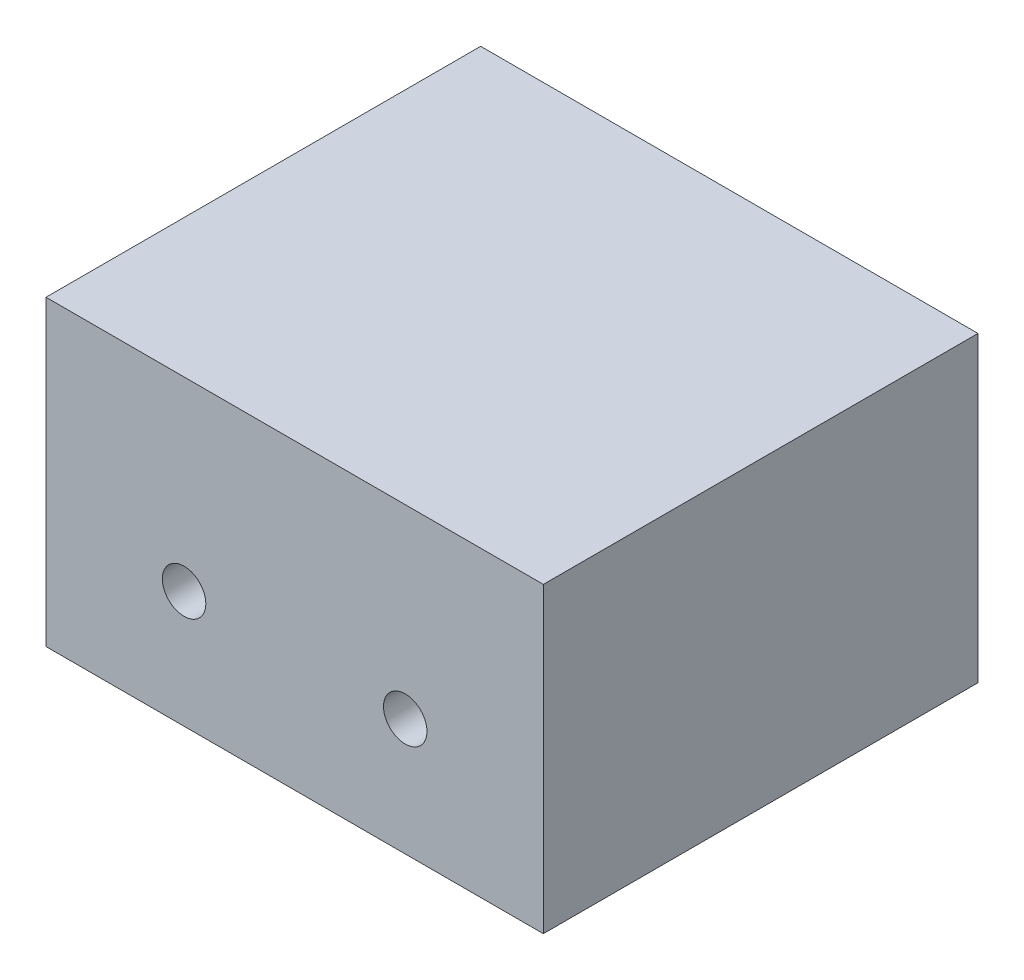
SolidWorks part; units mm, degrees
material "6061 Alloy"
ref_plane "Front Plane" through (0, 0, 0) normal (0, 0, 1) x (1, 0, 0)
ref_plane "Top Plane" through (0, 0, 0) normal (0, 1, 0) x (1, 0, 0)
ref_plane "Right Plane" through (0, 0, 0) normal (1, 0, 0) x (0, 0, -1)
sketch "Sketch1" plane through (0, 0, 0) normal (0, 1, 0) x (1, 0, 0)
  line L1 (-28.605, -25) -> (28.605, -25)
  line L2 (-28.605, -25) -> (-28.605, 25)
  line L3 (-28.605, 25) -> (28.605, 25)
  line L4 (28.605, -25) -> (28.605, 25)
  line L5 (-28.605, -25) -> (28.605, 25) construction
  line L6 (-28.605, 25) -> (28.605, -25) construction
  point P0 (0, 0)
  dimension "D1" = 57.21
  dimension "D2" = 50
extrude "Boss-Extrude1" add sketch "Sketch1" along normal blind 34.8
sketch "Sketch2" plane through (0, 0, 25) normal (0, 0, 1) x (1, 0, 0)
  line L0 (0, 34.8) -> (0, 0) construction
  line L1 (-28.605, 34.8) -> (28.605, 34.8) construction
  line L2 (-28.605, 0) -> (28.605, 0) construction
  circle A0 centre (-12.72, 13.45) radius 2.5
  dimension "D3" = 5
  dimension "D1" = 12.72
  dimension "D2" = 21.35
extrude "Cut-Extrude1" cut sketch "Sketch2" against normal through all
ref_plane "Plane1" through (0, 0, 0) normal (1, 0, 0) x (0, 0, -1)
mirror "Mirror1" about plane through (0, 0, 0) normal (1, 0, 0) of "Cut-Extrude1"
